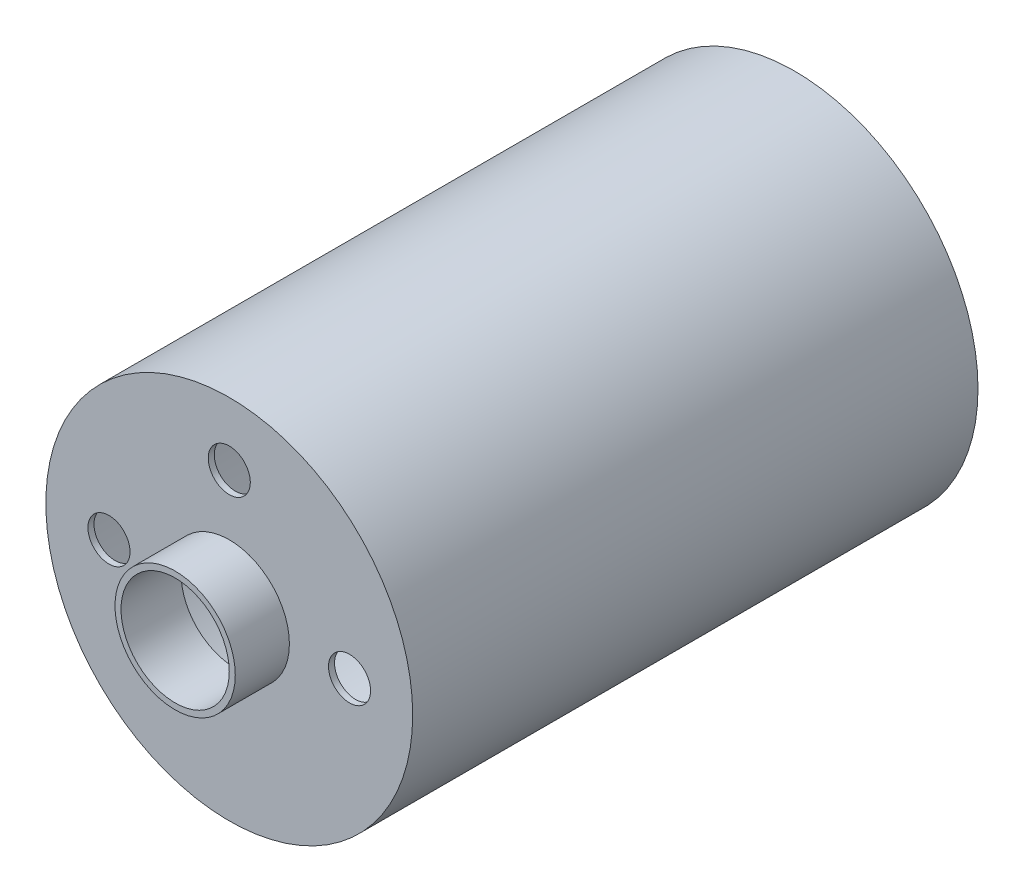
SolidWorks part; units mm, degrees
ref_plane "Front Plane" through (0, 0, 0) normal (0, 0, 1) x (1, 0, 0)
ref_plane "Top Plane" through (0, 0, 0) normal (0, 1, 0) x (1, 0, 0)
ref_plane "Right Plane" through (0, 0, 0) normal (1, 0, 0) x (0, 0, -1)
sketch "Sketch1" plane through (0, 0, 0) normal (0, 0, 1) x (1, 0, 0)
  circle A0 centre (0, 0) radius 15.25
  dimension "D1" = 30.5
extrude "Boss-Extrude1" add sketch "Sketch1" along normal mid plane 47
sketch "Sketch2" plane through (0, 0, 23.5) normal (0, 0, 1) x (1, 0, 0)
  circle A0 centre (0, 0) radius 5
  dimension "D1" = 10
extrude "Boss-Extrude2" add sketch "Sketch2" along normal blind 4.5
shell "Shell1" thickness 0.5
sketch "Sketch3" plane through (0, 0, 23.5) normal (0, 0, 1) x (1, 0, 0)
  circle A0 centre (-10, 0) radius 1.75
  circle A1 centre (0, 10) radius 1.75
  circle A2 centre (10, 0) radius 1.75
  point P9 (0, 0)
  dimension "D2" = 3.5
  dimension "D1" = 10
  dimension "D3" = 3
extrude "Cut-Extrude1" cut sketch "Sketch3" against normal blind 4.5
